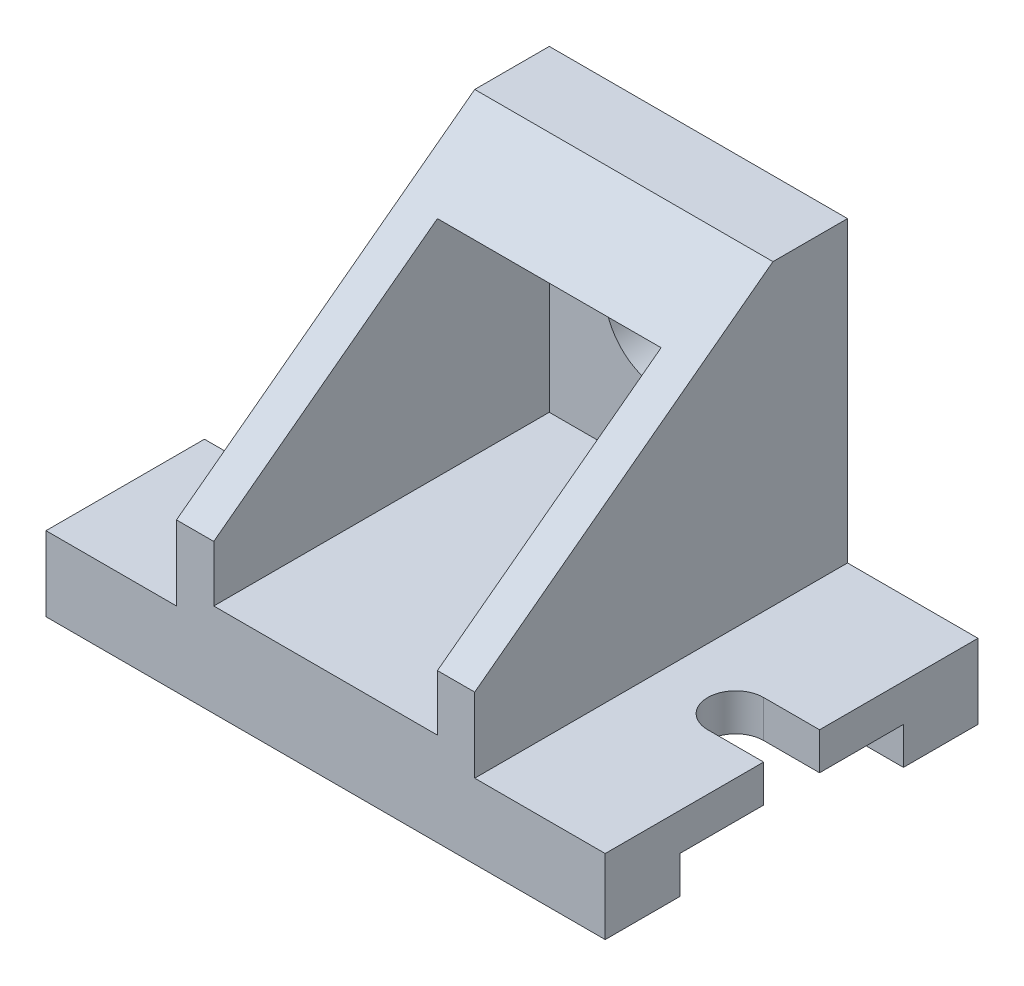
SolidWorks part; units mm, degrees
ref_plane "Front Plane" through (0, 0, 0) normal (0, 0, 1) x (1, 0, 0)
ref_plane "Top Plane" through (0, 0, 0) normal (0, 1, 0) x (1, 0, 0)
ref_plane "Right Plane" through (0, 0, 0) normal (1, 0, 0) x (0, 0, -1)
sketch "Sketch1" plane through (0, 0, 0) normal (0, 1, 0) x (1, 0, 0)
  line L1 (-75, 50) -> (75, 50)
  line L2 (-75, 50) -> (-75, -50)
  line L3 (-75, -50) -> (75, -50)
  line L4 (75, 50) -> (75, -50)
  line L5 (-75, 50) -> (75, -50) construction
  line L6 (-75, -50) -> (75, 50) construction
  point P0 (0, 0)
  dimension "D1" = 150
  dimension "D2" = 100
extrude "Boss-Extrude1" add sketch "Sketch1" along normal blind 20
sketch "Sketch2" plane through (-75, 0, 0) normal (-1, 0, 0) x (0, 0, 1)
  line L0 (0, 10) -> (0, 0) construction
  line L1 (-30, 10) -> (-30, 0)
  line L2 (30, 10) -> (30, 0)
  line L3 (-30, 0) -> (30, 0) construction
  line L4 (-50, 0) -> (50, 0) construction
  line L5 (-30, 10) -> (30, 10)
  line L6 (-30, 38.1095) -> (-30, -14.92) construction
  line L7 (0, 38.1095) -> (0, -14.92) construction
  line L8 (30, 38.1095) -> (30, -14.92) construction
  line L9 (-30, 0) -> (30, 0)
  dimension "D1" = 30
  dimension "D2" = 30
  dimension "D3" = 10
extrude "Cut-Extrude1" cut sketch "Sketch2" against normal through all
sketch "Sketch3" plane through (0, 20, 0) normal (0, 1, 0) x (1, 0, 0)
  line L0 (0, 61.671) -> (0, -62.0181) construction
  line L1 (-75, 50) -> (-75, -50) construction
  line L2 (-75, 7.5) -> (-75, -7.5)
  line L3 (75, 7.5) -> (75, -7.5)
  line L4 (60, -7.5) -> (75, -7.5)
  line L5 (-60, 7.5) -> (-75, 7.5)
  line L6 (-60, -7.5) -> (-75, -7.5)
  line L7 (60, 7.5) -> (75, 7.5)
  arc A0 (-60, -7.5) -> (-60, 7.5) centre (-60, 0) ccw
  arc A1 (60, -7.5) -> (60, 7.5) centre (60, 0) cw
  dimension "D2" = 15
extrude "Cut-Extrude2" cut sketch "Sketch3" against normal blind 20
sketch "Sketch8" plane through (0, 0, 0) normal (1, 0, 0) x (0, 0, -1)
  line L0 (50, 20) -> (50, 100)
  line L1 (50, 100) -> (30, 100)
  line L2 (30, 100) -> (-50, 40)
  line L3 (-50, 40) -> (-50, 20)
  line L4 (-50, 20) -> (50, 20)
  dimension "D1" = 80
  dimension "D2" = 20
  dimension "D3" = 20
extrude "Boss-Extrude3" add sketch "Sketch8" along normal mid plane 80
sketch "Sketch10" plane through (0, 0, 50) normal (0, 0, 1) x (1, 0, 0)
  line L0 (-75, 0) -> (75, 0) construction
  line L1 (-30, 25) -> (30, 25)
  line L2 (-30, 25) -> (-30, 85)
  line L3 (-30, 85) -> (30, 85)
  line L4 (30, 25) -> (30, 85)
  line L5 (-40, 100) -> (-40, 40) construction
  dimension "D1" = 25
  dimension "D2" = 60
  dimension "D3" = 60
  dimension "D4" = 10
extrude "Cut-Extrude3" cut sketch "Sketch10" against normal blind 90
sketch "Sketch11" plane through (0, 0, -50) normal (0, 0, -1) x (-1, 0, 0)
  line L0 (-75, 0) -> (75, 0) construction
  line L1 (40, 20) -> (40, 100) construction
  circle A0 centre (0, 60) radius 15
  dimension "D1" = 30
  dimension "D2" = 60
  dimension "D3" = 40
extrude "Cut-Extrude4" cut sketch "Sketch11" against normal blind 90
